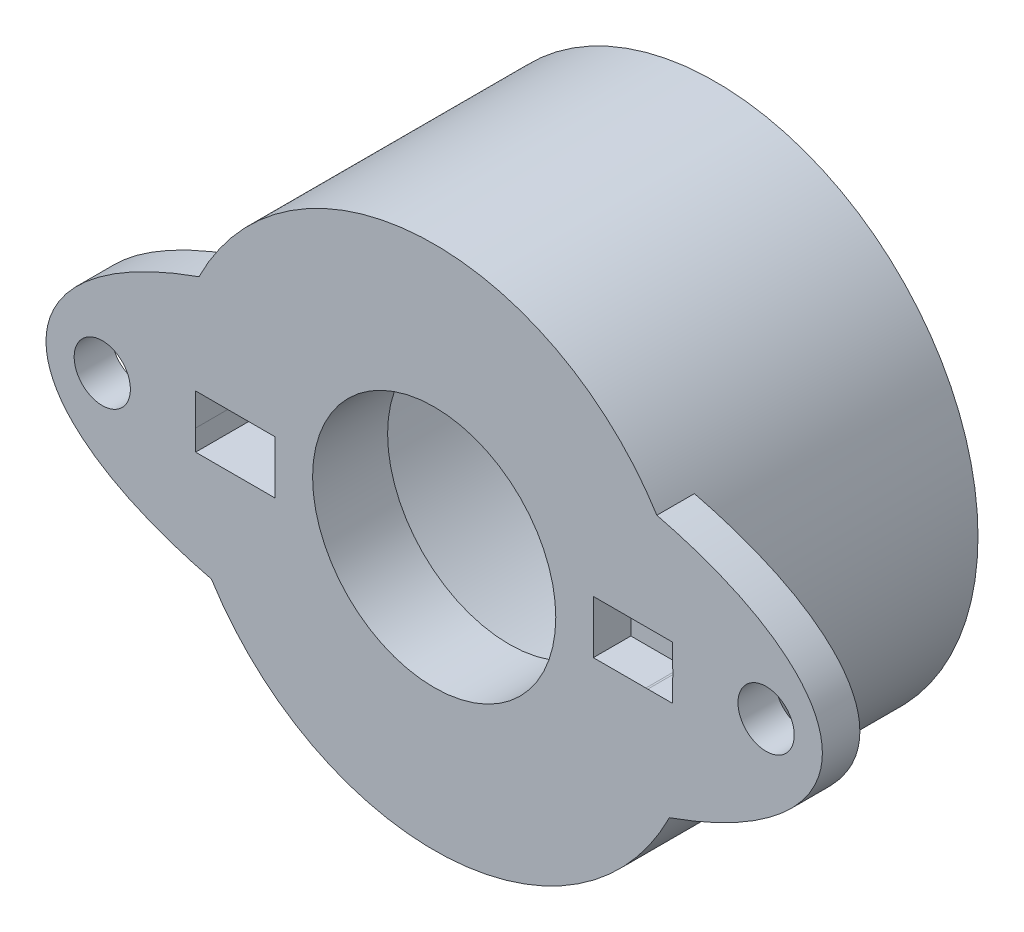
SolidWorks part; units mm, degrees
ref_plane "Front Plane" through (0, 0, 0) normal (0, 0, 1) x (1, 0, 0)
ref_plane "Top Plane" through (0, 0, 0) normal (0, 1, 0) x (1, 0, 0)
ref_plane "Right Plane" through (0, 0, 0) normal (1, 0, 0) x (0, 0, -1)
sketch "Çizim7" plane through (0, 0, 0) normal (0, 0, 1) x (1, 0, 0)
  circle A0 centre (0, 0) radius 14
extrude "Yükseklik-Ekstrüzyon3" add sketch "Çizim7" along normal blind 15
sketch "Çizim8" plane through (0, 0, 0) normal (0, 0, -1) x (-1, 0, 0)
  circle A0 centre (0, 0) radius 12.75
extrude "Kes-Ekstrüzyon2" cut sketch "Çizim8" against normal blind 13
sketch "Çizim10" plane through (0, 0, 15) normal (0, 0, 1) x (1, 0, 0)
  ellipse E0 centre (0, 0) end of major axis (-20.6965, -1.0118) minor radius 8.4518
extrude "Yükseklik-Ekstrüzyon5" add sketch "Çizim10" against normal blind 2
sketch "Çizim11" plane through (0, 0, 13) normal (0, 0, -1) x (-1, 0, 0)
  line L0 (-20.6932, 1.0689) -> (20.6988, -0.9547) construction
  circle A0 centre (-17.7001, 0.9225) radius 1.5
  circle A1 centre (17.7001, -0.8081) radius 1.5
  ellipse E0 centre (0, 0) end of major axis (20.6965, -1.0118) minor radius 8.4518 (-11.8762, 7.4133) -> (-12.5427, -6.2195) ccw construction
  ellipse E1 centre (0, 0) end of major axis (20.6965, -1.0118) minor radius 8.4518 (11.8762, -7.4133) -> (12.5427, 6.2195) ccw construction
extrude "Kes-Ekstrüzyon4" cut sketch "Çizim11" against normal blind 12 contours A0 | A1
sketch "Çizim12" plane through (0, 0, 13) normal (0, 0, -1) x (-1, 0, 0)
  circle A0 centre (-11.3408, 0.5388) radius 1.3964
  circle A1 centre (11.2314, -0.5573) radius 1.3964
extrude "Kes-Ekstrüzyon5" cut sketch "Çizim12" against normal blind 12 contours A0 | A1
sketch "Çizim13" plane through (0, 0, 13) normal (0, 0, -1) x (-1, 0, 0)
  line L0 (8.4878, -1.9716) -> (12.7212, -1.9716)
  line L1 (-12.7212, -0.8566) -> (-8.4878, -0.8566)
  line L2 (-12.7212, -0.8566) -> (-12.7212, 1.9719)
  line L3 (-12.7212, 1.9719) -> (-8.4878, 1.9719)
  line L4 (-8.4878, -0.8566) -> (-8.4878, 1.9719)
  line L5 (8.4878, -1.9716) -> (8.4878, 0.857)
  line L6 (8.4878, 0.857) -> (12.7212, 0.857)
  line L7 (12.7212, -1.9716) -> (12.7212, 0.857)
  circle A0 centre (0, 0) radius 12.75 construction
  circle M9 centre (11.2314, -0.5573) radius 1.3964
  circle M10 centre (0, 0) radius 12.75
extrude "Kes-Ekstrüzyon9" cut sketch "Çizim13" against normal blind 10 contours L7 L6 L5 L0 M10 M9 | L2 L1 L4 L3
sketch "Çizim17" plane through (0, 0, 13) normal (0, 0, -1) x (-1, 0, 0)
  circle A0 centre (0, 0) radius 6.4845
extrude "Kes-Ekstrüzyon10" cut sketch "Çizim17" against normal blind 10
sketch "Çizim18" plane through (0, 0, 13) normal (0, 0, -1) x (-1, 0, 0)
  circle A0 centre (0, 0) radius 12.75
extrude "Yükseklik-Ekstrüzyon6" add sketch "Çizim18" along normal blind 2
sketch "Çizim19" plane through (0, 0, 13) normal (0, 0, 1) x (1, 0, 0)
  circle A0 centre (0, 0) radius 6.4845
extrude "Kes-Ekstrüzyon11" cut sketch "Çizim19" against normal blind 15
sketch "Çizim20" plane through (0, 0, 15) normal (0, 0, 1) x (1, 0, 0)
  line L0 (-12.7212, 0.857) -> (-12.7212, 0.8566) construction
  line L1 (12.7212, -0.8566) -> (8.4878, -0.8566)
  line L2 (12.7212, -0.8566) -> (12.7212, 1.9719)
  line L3 (12.7212, 1.9719) -> (8.4878, 1.9719)
  line L4 (8.4878, -0.8566) -> (8.4878, 1.9719)
  line L5 (-8.4878, -1.9716) -> (-12.7212, -1.9716)
  line L6 (-8.4878, -1.9716) -> (-8.4878, 0.8568)
  line L7 (-8.4878, 0.8568) -> (-12.7212, 0.8568)
  line L8 (-12.7212, -1.9716) -> (-12.7212, 0.8568)
extrude "Kes-Ekstrüzyon12" cut sketch "Çizim20" against normal blind 15 contours L6 L5 L8 L7
